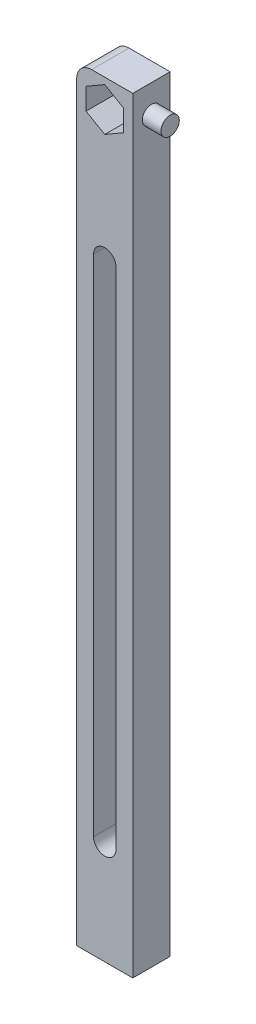
SolidWorks part; units mm, degrees
ref_plane "Alzado" through (0, 0, 0) normal (0, 0, 1) x (1, 0, 0)
ref_plane "Planta" through (0, 0, 0) normal (0, 1, 0) x (1, 0, 0)
ref_plane "Vista lateral" through (0, 0, 0) normal (1, 0, 0) x (0, 0, -1)
sketch "Croquis1" plane through (0, 0, 0) normal (0, 0, 1) x (1, 0, 0)
  line L0 (0, 0) -> (15, -15) construction
  line L1 (0, 0) -> (220, 0)
  line L2 (0, 0) -> (0, -220)
  line L3 (0, -220) -> (220, -220)
  line L4 (220, 0) -> (220, -220)
  line L5 (220, 0) -> (205, -15) construction
  line L6 (15, -15) -> (205, -15)
  line L7 (15, -15) -> (15, -205)
  line L8 (15, -205) -> (205, -205)
  line L9 (205, -15) -> (205, -205)
  line L10 (205, -15) -> (220, -15) construction
  line L11 (220, -15) -> (212.5, -7.5) construction
  line L12 (0, 0) -> (220, -220) construction
  line L13 (0, -220) -> (220, 0) construction
  line L14 (7.5, -7.5) -> (7.5, -212.5) construction
  line L15 (212.5, -13.2735) -> (217.5, -10.3868)
  line L16 (7.5, -13.2735) -> (12.5, -10.3868)
  line L17 (12.5, -10.3868) -> (12.5, -4.6132)
  line L18 (12.5, -4.6132) -> (7.5, -1.7265)
  line L19 (7.5, -1.7265) -> (2.5, -4.6132)
  line L20 (2.5, -4.6132) -> (2.5, -10.3868)
  line L21 (2.5, -10.3868) -> (7.5, -13.2735)
  line L22 (217.5, -10.3868) -> (217.5, -4.6132)
  line L23 (217.5, -4.6132) -> (212.5, -1.7265)
  line L24 (212.5, -1.7265) -> (207.5, -4.6132)
  line L25 (207.5, -4.6132) -> (207.5, -10.3868)
  line L26 (207.5, -10.3868) -> (212.5, -13.2735)
  line L27 (212.5, -218.2735) -> (217.5, -215.3868)
  line L28 (217.5, -215.3868) -> (217.5, -209.6132)
  line L29 (217.5, -209.6132) -> (212.5, -206.7265)
  line L30 (212.5, -206.7265) -> (207.5, -209.6132)
  line L31 (207.5, -209.6132) -> (207.5, -215.3868)
  line L32 (207.5, -215.3868) -> (212.5, -218.2735)
  line L33 (7.5, -218.2735) -> (12.5, -215.3868)
  line L34 (12.5, -215.3868) -> (12.5, -209.6132)
  line L35 (12.5, -209.6132) -> (7.5, -206.7265)
  line L36 (7.5, -206.7265) -> (2.5, -209.6132)
  line L37 (2.5, -209.6132) -> (2.5, -215.3868)
  line L38 (2.5, -215.3868) -> (7.5, -218.2735)
  circle A6 centre (7.5, -7.5) radius 5 construction
  dimension "D7" = 10
  dimension "D1" = 220
  dimension "D2" = 220
  dimension "D3" = 15
  dimension "D4" = 45
  dimension "D5" = 15
  dimension "D6" = 15
  dimension "D8" = 2
  dimension "D9" = 2
extrude "Saliente-Extruir1" add sketch "Croquis1" along normal blind 10
fillet "Redondeo2" radius 4 4 edges at (0, -220, 5) (220, -220, 5) (220, 0, 5) (0, 0, 5)
sketch "Croquis4" plane through (0, 0, 10) normal (0, 0, 1) x (1, 0, 0)
  line L0 (15, -15) -> (0, 0) construction
  line L1 (0, 0) -> (7.5, -7.5) construction
  line L2 (7.5, -7.5) -> (42.5, -7.5) construction
  line L3 (194.8375, 0) -> (225.1084, 0) construction
  line L4 (216, 0) -> (4, 0) construction
  line L5 (220, -16.4274) -> (220, 5.2916) construction
  line L6 (220, -216) -> (220, -4) construction
  line L7 (220, 0) -> (205, -15) construction
  line L8 (205, -15) -> (212.5, -7.5) construction
  line L9 (212.5, -7.5) -> (177.5, -7.5) construction
  line L10 (42.5, -7.5) -> (177.5, -7.5) construction
  line L11 (42.5, -4.5) -> (177.5, -4.5)
  line L12 (42.5, -10.5) -> (177.5, -10.5)
  line L13 (42.5, -215.5) -> (177.5, -215.5)
  line L14 (42.5, -209.5) -> (177.5, -209.5)
  line L15 (42.5, -212.5) -> (177.5, -212.5) construction
  arc A0 (42.5, -4.5) -> (42.5, -10.5) centre (42.5, -7.5) ccw
  arc A1 (177.5, -10.5) -> (177.5, -4.5) centre (177.5, -7.5) ccw
  arc A2 (42.5, -209.5) -> (42.5, -215.5) centre (42.5, -212.5) ccw
  arc A3 (177.5, -215.5) -> (177.5, -209.5) centre (177.5, -212.5) ccw
  point P17 (110, -7.5)
  point P27 (110, -212.5)
  dimension "D1" = 35
  dimension "D2" = 35
  dimension "D3" = 6
  dimension "D4" = 2
extrude "Cortar-Extruir4" cut sketch "Croquis4" against normal blind 10
sketch "Croquis5" plane through (0, 0, 10) normal (0, 0, 1) x (1, 0, 0)
  line L0 (15, -15.066) -> (15, -15) construction
  line L1 (15, -15) -> (15, -205) construction
  line L2 (15, -15) -> (0, 0) construction
  line L3 (0, 0) -> (7.5, -7.5) construction
  line L4 (7.5, -7.5) -> (7.5, -42.5) construction
  line L5 (15, -205) -> (7.5, -212.5) construction
  line L6 (7.5, -212.5) -> (7.5, -177.5) construction
  line L7 (7.5, -42.5) -> (7.5, -177.5) construction
  line L8 (10.5, -42.5) -> (10.5, -177.5)
  line L9 (4.5, -42.5) -> (4.5, -177.5)
  line L10 (209.5, -42.5) -> (209.5, -177.5)
  line L11 (215.5, -42.5) -> (215.5, -177.5)
  line L12 (212.5, -42.5) -> (212.5, -177.5) construction
  arc A0 (10.5, -42.5) -> (4.5, -42.5) centre (7.5, -42.5) ccw
  arc A1 (4.5, -177.5) -> (10.5, -177.5) centre (7.5, -177.5) ccw
  arc A2 (215.5, -42.5) -> (209.5, -42.5) centre (212.5, -42.5) ccw
  arc A3 (209.5, -177.5) -> (215.5, -177.5) centre (212.5, -177.5) ccw
  point P12 (7.5, -110)
  point P21 (212.5, -110)
  dimension "D1" = 35
  dimension "D2" = 35
  dimension "D3" = 6
  dimension "D4" = 2
extrude "Cortar-Extruir5" cut sketch "Croquis5" against normal blind 10
sketch "Croquis6" plane through (0, 0, 10) normal (0, 0, 1) x (1, 0, 0)
  line L0 (15, -15) -> (15, 0) construction
  line L1 (216, 0) -> (4, 0) construction
  line L2 (15, 0) -> (229.8324, 0) construction
  line L3 (229.8324, 0) -> (220, -37.6318) construction
  line L4 (220, -216) -> (220, -4) construction
  line L5 (220, -37.6318) -> (220, 9.5394) construction
  line L6 (4, -220) -> (216, -220) construction
  line L7 (229.8324, 0) -> (15, 0)
  line L8 (229.8324, 0) -> (229.8324, -220)
  line L9 (229.8324, -220) -> (15, -220)
  line L10 (15, 0) -> (15, -220)
extrude "Cortar-Extruir6" cut sketch "Croquis6" against normal blind 10
sketch "Croquis7" plane through (15, 0, 0) normal (1, 0, 0) x (0, 0, -1)
  line L0 (-5, 0) -> (-5, -7.5) construction
  line L1 (0, 0) -> (-10, 0) construction
  circle A0 centre (-5, -7.5) radius 2.45
  dimension "D2" = 4.9
  dimension "D1" = 7.5
extrude "Saliente-Extruir2" add sketch "Croquis7" along normal blind 5
sketch "Croquis11" plane through (0, 0, 10) normal (0, 0, 1) x (1, 0, 0)
  line L0 (0, -4) -> (0, -216) construction
  line L1 (15, -220) -> (0, -220)
  line L2 (15, -220) -> (15, -205)
  line L3 (15, -205) -> (0, -205)
  line L4 (0, -220) -> (0, -205)
  dimension "D1" = 15
extrude "Cortar-Extruir9" cut sketch "Croquis11" against normal blind 10
sketch "Croquis12" plane through (0, -205, 0) normal (0, -1, 0) x (1, 0, 0)
  line L0 (0, 5) -> (7.5, 5) construction
  line L1 (0, 0) -> (0, 10) construction
  circle A0 centre (7.5, 5) radius 2.5
  dimension "D2" = 5
  dimension "D1" = 7.5
extrude "Cortar-Extruir10" cut sketch "Croquis12" against normal blind 6
